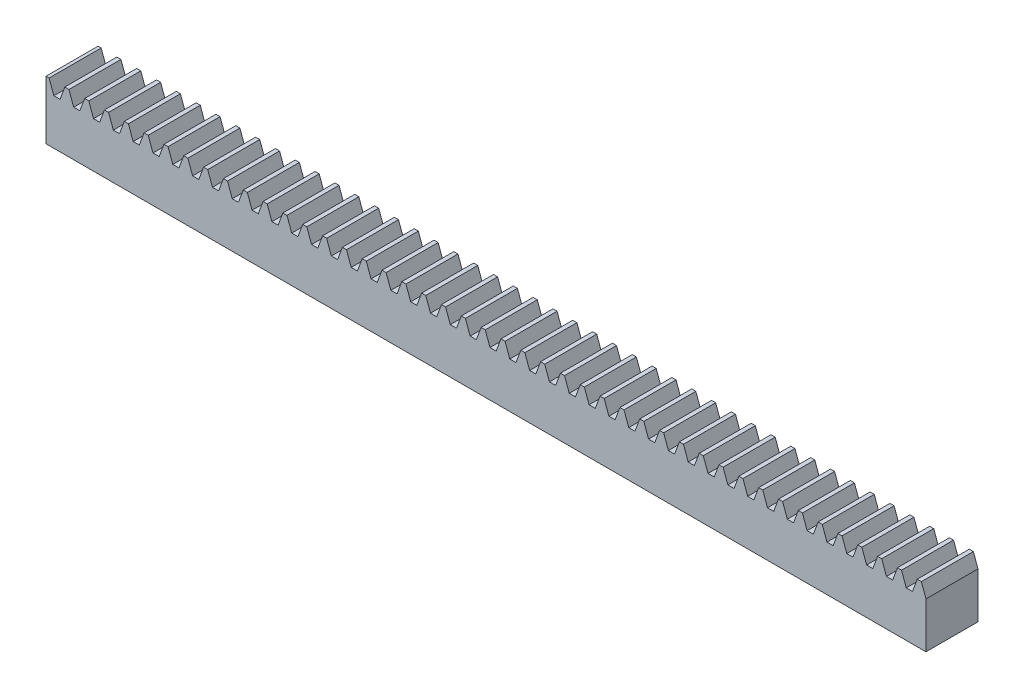
SolidWorks part; units mm, degrees
material "Nylon 101"
ref_plane "Front Plane" through (0, 0, 0) normal (0, 0, 1) x (1, 0, 0)
ref_plane "Top Plane" through (0, 0, 0) normal (0, 1, 0) x (1, 0, 0)
ref_plane "Right Plane" through (0, 0, 0) normal (1, 0, 0) x (0, 0, -1)
sketch "Sketch1" plane through (0, 0, 0) normal (0, 1, 0) x (1, 0, 0)
  line L0 (0, 0) -> (0, 4)
  line L1 (0, 4) -> (67.65, 4)
  line L2 (67.65, 4) -> (67.65, 0)
  line L3 (67.65, 0) -> (0, 0)
  dimension "D1" = 4
  dimension "D2" = 67.65
extrude "Boss-Extrude1" add sketch "Sketch1" along normal blind 4.5
sketch "Sketch2" plane through (0, 0, 0) normal (0, 0, 1) x (1, 0, 0)
  line L0 (0, 4) -> (67.65, 4) construction
  line L1 (0, 4.5) -> (0, 0) construction
  line L2 (67.65, 4.5) -> (67.65, 0) construction
  line L3 (0, 3.5) -> (67.65, 3.5) construction
  line L4 (0, 4.5) -> (67.65, 4.5) construction
  line L5 (0, 4.5) -> (0.239, 4.5) construction
  line L6 (0.239, 4.5) -> (0.603, 3.5)
  line L7 (0.603, 3.5) -> (0.842, 3.5)
  line L8 (1.081, 3.5) -> (1.445, 4.5)
  line L9 (1.445, 4.5) -> (1.684, 4.5) construction
  line L10 (0.842, 3.5) -> (1.081, 3.5)
  line L11 (0.239, 4.5) -> (1.445, 4.5)
  line L12 (1.763, 4.5) -> (2.127, 3.5)
  line L13 (2.127, 3.5) -> (2.366, 3.5)
  line L14 (2.605, 3.5) -> (2.969, 4.5)
  line L15 (2.366, 3.5) -> (2.605, 3.5)
  line L16 (1.763, 4.5) -> (2.969, 4.5)
  line L17 (1.524, 4.5) -> (1.763, 4.5) construction
  line L18 (2.969, 4.5) -> (3.208, 4.5) construction
  line L19 (3.287, 4.5) -> (3.651, 3.5)
  line L20 (3.651, 3.5) -> (3.89, 3.5)
  line L21 (4.129, 3.5) -> (4.493, 4.5)
  line L22 (3.89, 3.5) -> (4.129, 3.5)
  line L23 (3.287, 4.5) -> (4.493, 4.5)
  line L24 (3.048, 4.5) -> (3.287, 4.5) construction
  line L25 (4.493, 4.5) -> (4.732, 4.5) construction
  line L26 (4.811, 4.5) -> (5.175, 3.5)
  line L27 (5.175, 3.5) -> (5.414, 3.5)
  line L28 (5.653, 3.5) -> (6.017, 4.5)
  line L29 (5.414, 3.5) -> (5.653, 3.5)
  line L30 (4.811, 4.5) -> (6.017, 4.5)
  line L31 (4.572, 4.5) -> (4.811, 4.5) construction
  line L32 (6.017, 4.5) -> (6.256, 4.5) construction
  line L33 (6.335, 4.5) -> (6.699, 3.5)
  line L34 (6.699, 3.5) -> (6.938, 3.5)
  line L35 (7.177, 3.5) -> (7.541, 4.5)
  line L36 (6.938, 3.5) -> (7.177, 3.5)
  line L37 (6.335, 4.5) -> (7.541, 4.5)
  line L38 (6.096, 4.5) -> (6.335, 4.5) construction
  line L39 (7.541, 4.5) -> (7.78, 4.5) construction
  line L40 (7.859, 4.5) -> (8.223, 3.5)
  line L41 (8.223, 3.5) -> (8.462, 3.5)
  line L42 (8.701, 3.5) -> (9.065, 4.5)
  line L43 (8.462, 3.5) -> (8.701, 3.5)
  line L44 (7.859, 4.5) -> (9.065, 4.5)
  line L45 (7.62, 4.5) -> (7.859, 4.5) construction
  line L46 (9.065, 4.5) -> (9.304, 4.5) construction
  line L47 (9.383, 4.5) -> (9.747, 3.5)
  line L48 (9.747, 3.5) -> (9.986, 3.5)
  line L49 (10.225, 3.5) -> (10.589, 4.5)
  line L50 (9.986, 3.5) -> (10.225, 3.5)
  line L51 (9.383, 4.5) -> (10.589, 4.5)
  line L52 (9.144, 4.5) -> (9.383, 4.5) construction
  line L53 (10.589, 4.5) -> (10.828, 4.5) construction
  line L54 (10.907, 4.5) -> (11.271, 3.5)
  line L55 (11.271, 3.5) -> (11.51, 3.5)
  line L56 (11.749, 3.5) -> (12.113, 4.5)
  line L57 (11.51, 3.5) -> (11.749, 3.5)
  line L58 (10.907, 4.5) -> (12.113, 4.5)
  line L59 (10.668, 4.5) -> (10.907, 4.5) construction
  line L60 (12.113, 4.5) -> (12.352, 4.5) construction
  line L61 (12.431, 4.5) -> (12.795, 3.5)
  line L62 (12.795, 3.5) -> (13.034, 3.5)
  line L63 (13.273, 3.5) -> (13.637, 4.5)
  line L64 (13.034, 3.5) -> (13.273, 3.5)
  line L65 (12.431, 4.5) -> (13.637, 4.5)
  line L66 (12.192, 4.5) -> (12.431, 4.5) construction
  line L67 (13.637, 4.5) -> (13.876, 4.5) construction
  line L68 (13.955, 4.5) -> (14.319, 3.5)
  line L69 (14.319, 3.5) -> (14.558, 3.5)
  line L70 (14.797, 3.5) -> (15.161, 4.5)
  line L71 (14.558, 3.5) -> (14.797, 3.5)
  line L72 (13.955, 4.5) -> (15.161, 4.5)
  line L73 (13.716, 4.5) -> (13.955, 4.5) construction
  line L74 (15.161, 4.5) -> (15.4, 4.5) construction
  line L75 (15.479, 4.5) -> (15.843, 3.5)
  line L76 (15.843, 3.5) -> (16.082, 3.5)
  line L77 (16.321, 3.5) -> (16.685, 4.5)
  line L78 (16.082, 3.5) -> (16.321, 3.5)
  line L79 (15.479, 4.5) -> (16.685, 4.5)
  line L80 (15.24, 4.5) -> (15.479, 4.5) construction
  line L81 (16.685, 4.5) -> (16.924, 4.5) construction
  line L82 (17.003, 4.5) -> (17.367, 3.5)
  line L83 (17.367, 3.5) -> (17.606, 3.5)
  line L84 (17.845, 3.5) -> (18.209, 4.5)
  line L85 (17.606, 3.5) -> (17.845, 3.5)
  line L86 (17.003, 4.5) -> (18.209, 4.5)
  line L87 (16.764, 4.5) -> (17.003, 4.5) construction
  line L88 (18.209, 4.5) -> (18.448, 4.5) construction
  line L89 (18.527, 4.5) -> (18.891, 3.5)
  line L90 (18.891, 3.5) -> (19.13, 3.5)
  line L91 (19.369, 3.5) -> (19.733, 4.5)
  line L92 (19.13, 3.5) -> (19.369, 3.5)
  line L93 (18.527, 4.5) -> (19.733, 4.5)
  line L94 (18.288, 4.5) -> (18.527, 4.5) construction
  line L95 (19.733, 4.5) -> (19.972, 4.5) construction
  line L96 (20.051, 4.5) -> (20.415, 3.5)
  line L97 (20.415, 3.5) -> (20.654, 3.5)
  line L98 (20.893, 3.5) -> (21.257, 4.5)
  line L99 (20.654, 3.5) -> (20.893, 3.5)
  line L100 (20.051, 4.5) -> (21.257, 4.5)
  line L101 (19.812, 4.5) -> (20.051, 4.5) construction
  line L102 (21.257, 4.5) -> (21.496, 4.5) construction
  line L103 (21.575, 4.5) -> (21.939, 3.5)
  line L104 (21.939, 3.5) -> (22.178, 3.5)
  line L105 (22.417, 3.5) -> (22.781, 4.5)
  line L106 (22.178, 3.5) -> (22.417, 3.5)
  line L107 (21.575, 4.5) -> (22.781, 4.5)
  line L108 (21.336, 4.5) -> (21.575, 4.5) construction
  line L109 (22.781, 4.5) -> (23.02, 4.5) construction
  line L110 (23.099, 4.5) -> (23.463, 3.5)
  line L111 (23.463, 3.5) -> (23.702, 3.5)
  line L112 (23.941, 3.5) -> (24.305, 4.5)
  line L113 (23.702, 3.5) -> (23.941, 3.5)
  line L114 (23.099, 4.5) -> (24.305, 4.5)
  line L115 (22.86, 4.5) -> (23.099, 4.5) construction
  line L116 (24.305, 4.5) -> (24.544, 4.5) construction
  line L117 (24.623, 4.5) -> (24.987, 3.5)
  line L118 (24.987, 3.5) -> (25.226, 3.5)
  line L119 (25.465, 3.5) -> (25.829, 4.5)
  line L120 (25.226, 3.5) -> (25.465, 3.5)
  line L121 (24.623, 4.5) -> (25.829, 4.5)
  line L122 (24.384, 4.5) -> (24.623, 4.5) construction
  line L123 (25.829, 4.5) -> (26.068, 4.5) construction
  line L124 (26.147, 4.5) -> (26.511, 3.5)
  line L125 (26.511, 3.5) -> (26.75, 3.5)
  line L126 (26.989, 3.5) -> (27.353, 4.5)
  line L127 (26.75, 3.5) -> (26.989, 3.5)
  line L128 (26.147, 4.5) -> (27.353, 4.5)
  line L129 (25.908, 4.5) -> (26.147, 4.5) construction
  line L130 (27.353, 4.5) -> (27.592, 4.5) construction
  line L131 (27.671, 4.5) -> (28.035, 3.5)
  line L132 (28.035, 3.5) -> (28.274, 3.5)
  line L133 (28.513, 3.5) -> (28.877, 4.5)
  line L134 (28.274, 3.5) -> (28.513, 3.5)
  line L135 (27.671, 4.5) -> (28.877, 4.5)
  line L136 (27.432, 4.5) -> (27.671, 4.5) construction
  line L137 (28.877, 4.5) -> (29.116, 4.5) construction
  line L138 (29.195, 4.5) -> (29.559, 3.5)
  line L139 (29.559, 3.5) -> (29.798, 3.5)
  line L140 (30.037, 3.5) -> (30.401, 4.5)
  line L141 (29.798, 3.5) -> (30.037, 3.5)
  line L142 (29.195, 4.5) -> (30.401, 4.5)
  line L143 (28.956, 4.5) -> (29.195, 4.5) construction
  line L144 (30.401, 4.5) -> (30.64, 4.5) construction
  line L145 (30.719, 4.5) -> (31.083, 3.5)
  line L146 (31.083, 3.5) -> (31.322, 3.5)
  line L147 (31.561, 3.5) -> (31.925, 4.5)
  line L148 (31.322, 3.5) -> (31.561, 3.5)
  line L149 (30.719, 4.5) -> (31.925, 4.5)
  line L150 (30.48, 4.5) -> (30.719, 4.5) construction
  line L151 (31.925, 4.5) -> (32.164, 4.5) construction
  line L152 (32.243, 4.5) -> (32.607, 3.5)
  line L153 (32.607, 3.5) -> (32.846, 3.5)
  line L154 (33.085, 3.5) -> (33.449, 4.5)
  line L155 (32.846, 3.5) -> (33.085, 3.5)
  line L156 (32.243, 4.5) -> (33.449, 4.5)
  line L157 (32.004, 4.5) -> (32.243, 4.5) construction
  line L158 (33.449, 4.5) -> (33.688, 4.5) construction
  line L159 (33.767, 4.5) -> (34.131, 3.5)
  line L160 (34.131, 3.5) -> (34.37, 3.5)
  line L161 (34.609, 3.5) -> (34.973, 4.5)
  line L162 (34.37, 3.5) -> (34.609, 3.5)
  line L163 (33.767, 4.5) -> (34.973, 4.5)
  line L164 (33.528, 4.5) -> (33.767, 4.5) construction
  line L165 (34.973, 4.5) -> (35.212, 4.5) construction
  line L166 (35.291, 4.5) -> (35.655, 3.5)
  line L167 (35.655, 3.5) -> (35.894, 3.5)
  line L168 (36.133, 3.5) -> (36.497, 4.5)
  line L169 (35.894, 3.5) -> (36.133, 3.5)
  line L170 (35.291, 4.5) -> (36.497, 4.5)
  line L171 (35.052, 4.5) -> (35.291, 4.5) construction
  line L172 (36.497, 4.5) -> (36.736, 4.5) construction
  line L173 (36.815, 4.5) -> (37.179, 3.5)
  line L174 (37.179, 3.5) -> (37.418, 3.5)
  line L175 (37.657, 3.5) -> (38.021, 4.5)
  line L176 (37.418, 3.5) -> (37.657, 3.5)
  line L177 (36.815, 4.5) -> (38.021, 4.5)
  line L178 (36.576, 4.5) -> (36.815, 4.5) construction
  line L179 (38.021, 4.5) -> (38.26, 4.5) construction
  line L180 (38.339, 4.5) -> (38.703, 3.5)
  line L181 (38.703, 3.5) -> (38.942, 3.5)
  line L182 (39.181, 3.5) -> (39.545, 4.5)
  line L183 (38.942, 3.5) -> (39.181, 3.5)
  line L184 (38.339, 4.5) -> (39.545, 4.5)
  line L185 (38.1, 4.5) -> (38.339, 4.5) construction
  line L186 (39.545, 4.5) -> (39.784, 4.5) construction
  line L187 (39.863, 4.5) -> (40.227, 3.5)
  line L188 (40.227, 3.5) -> (40.466, 3.5)
  line L189 (40.705, 3.5) -> (41.069, 4.5)
  line L190 (40.466, 3.5) -> (40.705, 3.5)
  line L191 (39.863, 4.5) -> (41.069, 4.5)
  line L192 (39.624, 4.5) -> (39.863, 4.5) construction
  line L193 (41.069, 4.5) -> (41.308, 4.5) construction
  line L194 (41.387, 4.5) -> (41.751, 3.5)
  line L195 (41.751, 3.5) -> (41.99, 3.5)
  line L196 (42.229, 3.5) -> (42.593, 4.5)
  line L197 (41.99, 3.5) -> (42.229, 3.5)
  line L198 (41.387, 4.5) -> (42.593, 4.5)
  line L199 (41.148, 4.5) -> (41.387, 4.5) construction
  line L200 (42.593, 4.5) -> (42.832, 4.5) construction
  line L201 (42.911, 4.5) -> (43.275, 3.5)
  line L202 (43.275, 3.5) -> (43.514, 3.5)
  line L203 (43.753, 3.5) -> (44.117, 4.5)
  line L204 (43.514, 3.5) -> (43.753, 3.5)
  line L205 (42.911, 4.5) -> (44.117, 4.5)
  line L206 (42.672, 4.5) -> (42.911, 4.5) construction
  line L207 (44.117, 4.5) -> (44.356, 4.5) construction
  line L208 (44.435, 4.5) -> (44.799, 3.5)
  line L209 (44.799, 3.5) -> (45.038, 3.5)
  line L210 (45.277, 3.5) -> (45.641, 4.5)
  line L211 (45.038, 3.5) -> (45.277, 3.5)
  line L212 (44.435, 4.5) -> (45.641, 4.5)
  line L213 (44.196, 4.5) -> (44.435, 4.5) construction
  line L214 (45.641, 4.5) -> (45.88, 4.5) construction
  line L215 (45.959, 4.5) -> (46.323, 3.5)
  line L216 (46.323, 3.5) -> (46.562, 3.5)
  line L217 (46.801, 3.5) -> (47.165, 4.5)
  line L218 (46.562, 3.5) -> (46.801, 3.5)
  line L219 (45.959, 4.5) -> (47.165, 4.5)
  line L220 (45.72, 4.5) -> (45.959, 4.5) construction
  line L221 (47.165, 4.5) -> (47.404, 4.5) construction
  line L222 (47.483, 4.5) -> (47.847, 3.5)
  line L223 (47.847, 3.5) -> (48.086, 3.5)
  line L224 (48.325, 3.5) -> (48.689, 4.5)
  line L225 (48.086, 3.5) -> (48.325, 3.5)
  line L226 (47.483, 4.5) -> (48.689, 4.5)
  line L227 (47.244, 4.5) -> (47.483, 4.5) construction
  line L228 (48.689, 4.5) -> (48.928, 4.5) construction
  line L229 (49.007, 4.5) -> (49.371, 3.5)
  line L230 (49.371, 3.5) -> (49.61, 3.5)
  line L231 (49.849, 3.5) -> (50.213, 4.5)
  line L232 (49.61, 3.5) -> (49.849, 3.5)
  line L233 (49.007, 4.5) -> (50.213, 4.5)
  line L234 (48.768, 4.5) -> (49.007, 4.5) construction
  line L235 (50.213, 4.5) -> (50.452, 4.5) construction
  line L236 (50.531, 4.5) -> (50.895, 3.5)
  line L237 (50.895, 3.5) -> (51.134, 3.5)
  line L238 (51.373, 3.5) -> (51.737, 4.5)
  line L239 (51.134, 3.5) -> (51.373, 3.5)
  line L240 (50.531, 4.5) -> (51.737, 4.5)
  line L241 (50.292, 4.5) -> (50.531, 4.5) construction
  line L242 (51.737, 4.5) -> (51.976, 4.5) construction
  line L243 (52.055, 4.5) -> (52.419, 3.5)
  line L244 (52.419, 3.5) -> (52.658, 3.5)
  line L245 (52.897, 3.5) -> (53.261, 4.5)
  line L246 (52.658, 3.5) -> (52.897, 3.5)
  line L247 (52.055, 4.5) -> (53.261, 4.5)
  line L248 (51.816, 4.5) -> (52.055, 4.5) construction
  line L249 (53.261, 4.5) -> (53.5, 4.5) construction
  line L250 (53.579, 4.5) -> (53.943, 3.5)
  line L251 (53.943, 3.5) -> (54.182, 3.5)
  line L252 (54.421, 3.5) -> (54.785, 4.5)
  line L253 (54.182, 3.5) -> (54.421, 3.5)
  line L254 (53.579, 4.5) -> (54.785, 4.5)
  line L255 (53.34, 4.5) -> (53.579, 4.5) construction
  line L256 (54.785, 4.5) -> (55.024, 4.5) construction
  line L257 (55.103, 4.5) -> (55.467, 3.5)
  line L258 (55.467, 3.5) -> (55.706, 3.5)
  line L259 (55.945, 3.5) -> (56.309, 4.5)
  line L260 (55.706, 3.5) -> (55.945, 3.5)
  line L261 (55.103, 4.5) -> (56.309, 4.5)
  line L262 (54.864, 4.5) -> (55.103, 4.5) construction
  line L263 (56.309, 4.5) -> (56.548, 4.5) construction
  line L264 (56.627, 4.5) -> (56.991, 3.5)
  line L265 (56.991, 3.5) -> (57.23, 3.5)
  line L266 (57.469, 3.5) -> (57.833, 4.5)
  line L267 (57.23, 3.5) -> (57.469, 3.5)
  line L268 (56.627, 4.5) -> (57.833, 4.5)
  line L269 (56.388, 4.5) -> (56.627, 4.5) construction
  line L270 (57.833, 4.5) -> (58.072, 4.5) construction
  line L271 (58.151, 4.5) -> (58.515, 3.5)
  line L272 (58.515, 3.5) -> (58.754, 3.5)
  line L273 (58.993, 3.5) -> (59.357, 4.5)
  line L274 (58.754, 3.5) -> (58.993, 3.5)
  line L275 (58.151, 4.5) -> (59.357, 4.5)
  line L276 (57.912, 4.5) -> (58.151, 4.5) construction
  line L277 (59.357, 4.5) -> (59.596, 4.5) construction
  line L278 (59.675, 4.5) -> (60.039, 3.5)
  line L279 (60.039, 3.5) -> (60.278, 3.5)
  line L280 (60.517, 3.5) -> (60.881, 4.5)
  line L281 (60.278, 3.5) -> (60.517, 3.5)
  line L282 (59.675, 4.5) -> (60.881, 4.5)
  line L283 (59.436, 4.5) -> (59.675, 4.5) construction
  line L284 (60.881, 4.5) -> (61.12, 4.5) construction
  line L285 (61.199, 4.5) -> (61.563, 3.5)
  line L286 (61.563, 3.5) -> (61.802, 3.5)
  line L287 (62.041, 3.5) -> (62.405, 4.5)
  line L288 (61.802, 3.5) -> (62.041, 3.5)
  line L289 (61.199, 4.5) -> (62.405, 4.5)
  line L290 (60.96, 4.5) -> (61.199, 4.5) construction
  line L291 (62.405, 4.5) -> (62.644, 4.5) construction
  line L292 (62.723, 4.5) -> (63.087, 3.5)
  line L293 (63.087, 3.5) -> (63.326, 3.5)
  line L294 (63.565, 3.5) -> (63.929, 4.5)
  line L295 (63.326, 3.5) -> (63.565, 3.5)
  line L296 (62.723, 4.5) -> (63.929, 4.5)
  line L297 (62.484, 4.5) -> (62.723, 4.5) construction
  line L298 (63.929, 4.5) -> (64.168, 4.5) construction
  line L299 (64.247, 4.5) -> (64.611, 3.5)
  line L300 (64.611, 3.5) -> (64.85, 3.5)
  line L301 (65.089, 3.5) -> (65.453, 4.5)
  line L302 (64.85, 3.5) -> (65.089, 3.5)
  line L303 (64.247, 4.5) -> (65.453, 4.5)
  line L304 (64.008, 4.5) -> (64.247, 4.5) construction
  line L305 (65.453, 4.5) -> (65.692, 4.5) construction
  line L306 (65.771, 4.5) -> (66.135, 3.5)
  line L307 (66.135, 3.5) -> (66.374, 3.5)
  line L308 (66.613, 3.5) -> (66.977, 4.5)
  line L309 (66.374, 3.5) -> (66.613, 3.5)
  line L310 (65.771, 4.5) -> (66.977, 4.5)
  line L311 (65.532, 4.5) -> (65.771, 4.5) construction
  line L312 (66.977, 4.5) -> (67.216, 4.5) construction
  line L313 (67.295, 4.5) -> (67.659, 3.5)
  line L314 (67.659, 3.5) -> (67.898, 3.5)
  line L315 (68.137, 3.5) -> (68.501, 4.5)
  line L316 (67.898, 3.5) -> (68.137, 3.5)
  line L317 (67.295, 4.5) -> (68.501, 4.5)
  line L318 (67.056, 4.5) -> (67.295, 4.5) construction
  line L319 (68.501, 4.5) -> (68.74, 4.5) construction
  line L320 (68.819, 4.5) -> (69.183, 3.5)
  line L321 (69.183, 3.5) -> (69.422, 3.5)
  line L322 (69.661, 3.5) -> (70.025, 4.5)
  line L323 (69.422, 3.5) -> (69.661, 3.5)
  line L324 (68.819, 4.5) -> (70.025, 4.5)
  line L325 (68.58, 4.5) -> (68.819, 4.5) construction
  line L326 (70.025, 4.5) -> (70.264, 4.5) construction
  line L327 (70.343, 4.5) -> (70.707, 3.5)
  line L328 (70.707, 3.5) -> (70.946, 3.5)
  line L329 (71.185, 3.5) -> (71.549, 4.5)
  line L330 (70.946, 3.5) -> (71.185, 3.5)
  line L331 (70.343, 4.5) -> (71.549, 4.5)
  line L332 (70.104, 4.5) -> (70.343, 4.5) construction
  line L333 (71.549, 4.5) -> (71.788, 4.5) construction
  line L334 (71.867, 4.5) -> (72.231, 3.5)
  line L335 (72.231, 3.5) -> (72.47, 3.5)
  line L336 (72.709, 3.5) -> (73.073, 4.5)
  line L337 (72.47, 3.5) -> (72.709, 3.5)
  line L338 (71.867, 4.5) -> (73.073, 4.5)
  line L339 (71.628, 4.5) -> (71.867, 4.5) construction
  line L340 (73.073, 4.5) -> (73.312, 4.5) construction
  line L341 (73.391, 4.5) -> (73.755, 3.5)
  line L342 (73.755, 3.5) -> (73.994, 3.5)
  line L343 (74.233, 3.5) -> (74.597, 4.5)
  line L344 (73.994, 3.5) -> (74.233, 3.5)
  line L345 (73.391, 4.5) -> (74.597, 4.5)
  line L346 (73.152, 4.5) -> (73.391, 4.5) construction
  line L347 (74.597, 4.5) -> (74.836, 4.5) construction
  line L348 (74.915, 4.5) -> (75.279, 3.5)
  line L349 (75.279, 3.5) -> (75.518, 3.5)
  line L350 (75.757, 3.5) -> (76.121, 4.5)
  line L351 (75.518, 3.5) -> (75.757, 3.5)
  line L352 (74.915, 4.5) -> (76.121, 4.5)
  line L353 (74.676, 4.5) -> (74.915, 4.5) construction
  line L354 (76.121, 4.5) -> (76.36, 4.5) construction
  line L355 (76.439, 4.5) -> (76.803, 3.5)
  line L356 (76.803, 3.5) -> (77.042, 3.5)
  line L357 (77.281, 3.5) -> (77.645, 4.5)
  line L358 (77.042, 3.5) -> (77.281, 3.5)
  line L359 (76.439, 4.5) -> (77.645, 4.5)
  line L360 (76.2, 4.5) -> (76.439, 4.5) construction
  line L361 (77.645, 4.5) -> (77.884, 4.5) construction
  line L362 (77.963, 4.5) -> (78.327, 3.5)
  line L363 (78.327, 3.5) -> (78.566, 3.5)
  line L364 (78.805, 3.5) -> (79.169, 4.5)
  line L365 (78.566, 3.5) -> (78.805, 3.5)
  line L366 (77.963, 4.5) -> (79.169, 4.5)
  line L367 (77.724, 4.5) -> (77.963, 4.5) construction
  line L368 (79.169, 4.5) -> (79.408, 4.5) construction
  line L369 (79.487, 4.5) -> (79.851, 3.5)
  line L370 (79.851, 3.5) -> (80.09, 3.5)
  line L371 (80.329, 3.5) -> (80.693, 4.5)
  line L372 (80.09, 3.5) -> (80.329, 3.5)
  line L373 (79.487, 4.5) -> (80.693, 4.5)
  line L374 (79.248, 4.5) -> (79.487, 4.5) construction
  line L375 (80.693, 4.5) -> (80.932, 4.5) construction
  line L376 (81.011, 4.5) -> (81.375, 3.5)
  line L377 (81.375, 3.5) -> (81.614, 3.5)
  line L378 (81.853, 3.5) -> (82.217, 4.5)
  line L379 (81.614, 3.5) -> (81.853, 3.5)
  line L380 (81.011, 4.5) -> (82.217, 4.5)
  line L381 (80.772, 4.5) -> (81.011, 4.5) construction
  line L382 (82.217, 4.5) -> (82.456, 4.5) construction
  line L383 (82.535, 4.5) -> (82.899, 3.5)
  line L384 (82.899, 3.5) -> (83.138, 3.5)
  line L385 (83.377, 3.5) -> (83.741, 4.5)
  line L386 (83.138, 3.5) -> (83.377, 3.5)
  line L387 (82.535, 4.5) -> (83.741, 4.5)
  line L388 (82.296, 4.5) -> (82.535, 4.5) construction
  line L389 (83.741, 4.5) -> (83.98, 4.5) construction
  line L390 (84.059, 4.5) -> (84.423, 3.5)
  line L391 (84.423, 3.5) -> (84.662, 3.5)
  line L392 (84.901, 3.5) -> (85.265, 4.5)
  line L393 (84.662, 3.5) -> (84.901, 3.5)
  line L394 (84.059, 4.5) -> (85.265, 4.5)
  line L395 (83.82, 4.5) -> (84.059, 4.5) construction
  line L396 (85.265, 4.5) -> (85.504, 4.5) construction
  line L397 (85.583, 4.5) -> (85.947, 3.5)
  line L398 (85.947, 3.5) -> (86.186, 3.5)
  line L399 (86.425, 3.5) -> (86.789, 4.5)
  line L400 (86.186, 3.5) -> (86.425, 3.5)
  line L401 (85.583, 4.5) -> (86.789, 4.5)
  line L402 (85.344, 4.5) -> (85.583, 4.5) construction
  line L403 (86.789, 4.5) -> (87.028, 4.5) construction
  line L404 (87.107, 4.5) -> (87.471, 3.5)
  line L405 (87.471, 3.5) -> (87.71, 3.5)
  line L406 (87.949, 3.5) -> (88.313, 4.5)
  line L407 (87.71, 3.5) -> (87.949, 3.5)
  line L408 (87.107, 4.5) -> (88.313, 4.5)
  line L409 (86.868, 4.5) -> (87.107, 4.5) construction
  line L410 (88.313, 4.5) -> (88.552, 4.5) construction
  line L411 (88.631, 4.5) -> (88.995, 3.5)
  line L412 (88.995, 3.5) -> (89.234, 3.5)
  line L413 (89.473, 3.5) -> (89.837, 4.5)
  line L414 (89.234, 3.5) -> (89.473, 3.5)
  line L415 (88.631, 4.5) -> (89.837, 4.5)
  line L416 (88.392, 4.5) -> (88.631, 4.5) construction
  line L417 (89.837, 4.5) -> (90.076, 4.5) construction
  line L418 (90.155, 4.5) -> (90.519, 3.5)
  line L419 (90.519, 3.5) -> (90.758, 3.5)
  line L420 (90.997, 3.5) -> (91.361, 4.5)
  line L421 (90.758, 3.5) -> (90.997, 3.5)
  line L422 (90.155, 4.5) -> (91.361, 4.5)
  line L423 (89.916, 4.5) -> (90.155, 4.5) construction
  line L424 (91.361, 4.5) -> (91.6, 4.5) construction
  line L425 (91.679, 4.5) -> (92.043, 3.5)
  line L426 (92.043, 3.5) -> (92.282, 3.5)
  line L427 (92.521, 3.5) -> (92.885, 4.5)
  line L428 (92.282, 3.5) -> (92.521, 3.5)
  line L429 (91.679, 4.5) -> (92.885, 4.5)
  line L430 (91.44, 4.5) -> (91.679, 4.5) construction
  line L431 (92.885, 4.5) -> (93.124, 4.5) construction
  line L432 (93.203, 4.5) -> (93.567, 3.5)
  line L433 (93.567, 3.5) -> (93.806, 3.5)
  line L434 (94.045, 3.5) -> (94.409, 4.5)
  line L435 (93.806, 3.5) -> (94.045, 3.5)
  line L436 (93.203, 4.5) -> (94.409, 4.5)
  line L437 (92.964, 4.5) -> (93.203, 4.5) construction
  line L438 (94.409, 4.5) -> (94.648, 4.5) construction
  line L439 (94.727, 4.5) -> (95.091, 3.5)
  line L440 (95.091, 3.5) -> (95.33, 3.5)
  line L441 (95.569, 3.5) -> (95.933, 4.5)
  line L442 (95.33, 3.5) -> (95.569, 3.5)
  line L443 (94.727, 4.5) -> (95.933, 4.5)
  line L444 (94.488, 4.5) -> (94.727, 4.5) construction
  line L445 (95.933, 4.5) -> (96.172, 4.5) construction
  line L446 (96.251, 4.5) -> (96.615, 3.5)
  line L447 (96.615, 3.5) -> (96.854, 3.5)
  line L448 (97.093, 3.5) -> (97.457, 4.5)
  line L449 (96.854, 3.5) -> (97.093, 3.5)
  line L450 (96.251, 4.5) -> (97.457, 4.5)
  line L451 (96.012, 4.5) -> (96.251, 4.5) construction
  line L452 (97.457, 4.5) -> (97.696, 4.5) construction
  line L453 (97.775, 4.5) -> (98.139, 3.5)
  line L454 (98.139, 3.5) -> (98.378, 3.5)
  line L455 (98.617, 3.5) -> (98.981, 4.5)
  line L456 (98.378, 3.5) -> (98.617, 3.5)
  line L457 (97.775, 4.5) -> (98.981, 4.5)
  line L458 (97.536, 4.5) -> (97.775, 4.5) construction
  line L459 (98.981, 4.5) -> (99.22, 4.5) construction
  line L460 (99.299, 4.5) -> (99.663, 3.5)
  line L461 (99.663, 3.5) -> (99.902, 3.5)
  line L462 (100.141, 3.5) -> (100.505, 4.5)
  line L463 (99.902, 3.5) -> (100.141, 3.5)
  line L464 (99.299, 4.5) -> (100.505, 4.5)
  line L465 (99.06, 4.5) -> (99.299, 4.5) construction
  line L466 (100.505, 4.5) -> (100.744, 4.5) construction
  line L467 (100.823, 4.5) -> (101.187, 3.5)
  line L468 (101.187, 3.5) -> (101.426, 3.5)
  line L469 (101.665, 3.5) -> (102.029, 4.5)
  line L470 (101.426, 3.5) -> (101.665, 3.5)
  line L471 (100.823, 4.5) -> (102.029, 4.5)
  line L472 (100.584, 4.5) -> (100.823, 4.5) construction
  line L473 (102.029, 4.5) -> (102.268, 4.5) construction
  line L474 (102.347, 4.5) -> (102.711, 3.5)
  line L475 (102.711, 3.5) -> (102.95, 3.5)
  line L476 (103.189, 3.5) -> (103.553, 4.5)
  line L477 (102.95, 3.5) -> (103.189, 3.5)
  line L478 (102.347, 4.5) -> (103.553, 4.5)
  line L479 (102.108, 4.5) -> (102.347, 4.5) construction
  line L480 (103.553, 4.5) -> (103.792, 4.5) construction
  line L481 (103.871, 4.5) -> (104.235, 3.5)
  line L482 (104.235, 3.5) -> (104.474, 3.5)
  line L483 (104.713, 3.5) -> (105.077, 4.5)
  line L484 (104.474, 3.5) -> (104.713, 3.5)
  line L485 (103.871, 4.5) -> (105.077, 4.5)
  line L486 (103.632, 4.5) -> (103.871, 4.5) construction
  line L487 (105.077, 4.5) -> (105.316, 4.5) construction
  line L488 (105.395, 4.5) -> (105.759, 3.5)
  line L489 (105.759, 3.5) -> (105.998, 3.5)
  line L490 (106.237, 3.5) -> (106.601, 4.5)
  line L491 (105.998, 3.5) -> (106.237, 3.5)
  line L492 (105.395, 4.5) -> (106.601, 4.5)
  line L493 (105.156, 4.5) -> (105.395, 4.5) construction
  line L494 (106.601, 4.5) -> (106.84, 4.5) construction
  line L495 (106.919, 4.5) -> (107.283, 3.5)
  line L496 (107.283, 3.5) -> (107.522, 3.5)
  line L497 (107.761, 3.5) -> (108.125, 4.5)
  line L498 (107.522, 3.5) -> (107.761, 3.5)
  line L499 (106.919, 4.5) -> (108.125, 4.5)
  line L500 (106.68, 4.5) -> (106.919, 4.5) construction
  line L501 (108.125, 4.5) -> (108.364, 4.5) construction
  line L502 (108.443, 4.5) -> (108.807, 3.5)
  line L503 (108.807, 3.5) -> (109.046, 3.5)
  line L504 (109.285, 3.5) -> (109.649, 4.5)
  line L505 (109.046, 3.5) -> (109.285, 3.5)
  line L506 (108.443, 4.5) -> (109.649, 4.5)
  line L507 (108.204, 4.5) -> (108.443, 4.5) construction
  line L508 (109.649, 4.5) -> (109.888, 4.5) construction
  line L509 (109.967, 4.5) -> (110.331, 3.5)
  line L510 (110.331, 3.5) -> (110.57, 3.5)
  line L511 (110.809, 3.5) -> (111.173, 4.5)
  line L512 (110.57, 3.5) -> (110.809, 3.5)
  line L513 (109.967, 4.5) -> (111.173, 4.5)
  line L514 (109.728, 4.5) -> (109.967, 4.5) construction
  line L515 (111.173, 4.5) -> (111.412, 4.5) construction
  line L516 (111.491, 4.5) -> (111.855, 3.5)
  line L517 (111.855, 3.5) -> (112.094, 3.5)
  line L518 (112.333, 3.5) -> (112.697, 4.5)
  line L519 (112.094, 3.5) -> (112.333, 3.5)
  line L520 (111.491, 4.5) -> (112.697, 4.5)
  line L521 (111.252, 4.5) -> (111.491, 4.5) construction
  line L522 (112.697, 4.5) -> (112.936, 4.5) construction
  line L523 (113.015, 4.5) -> (113.379, 3.5)
  line L524 (113.379, 3.5) -> (113.618, 3.5)
  line L525 (113.857, 3.5) -> (114.221, 4.5)
  line L526 (113.618, 3.5) -> (113.857, 3.5)
  line L527 (113.015, 4.5) -> (114.221, 4.5)
  line L528 (112.776, 4.5) -> (113.015, 4.5) construction
  line L529 (114.221, 4.5) -> (114.46, 4.5) construction
  line L530 (114.539, 4.5) -> (114.903, 3.5)
  line L531 (114.903, 3.5) -> (115.142, 3.5)
  line L532 (115.381, 3.5) -> (115.745, 4.5)
  line L533 (115.142, 3.5) -> (115.381, 3.5)
  line L534 (114.539, 4.5) -> (115.745, 4.5)
  line L535 (114.3, 4.5) -> (114.539, 4.5) construction
  line L536 (115.745, 4.5) -> (115.984, 4.5) construction
  line L537 (116.063, 4.5) -> (116.427, 3.5)
  line L538 (116.427, 3.5) -> (116.666, 3.5)
  line L539 (116.905, 3.5) -> (117.269, 4.5)
  line L540 (116.666, 3.5) -> (116.905, 3.5)
  line L541 (116.063, 4.5) -> (117.269, 4.5)
  line L542 (115.824, 4.5) -> (116.063, 4.5) construction
  line L543 (117.269, 4.5) -> (117.508, 4.5) construction
  line L544 (117.587, 4.5) -> (117.951, 3.5)
  line L545 (117.951, 3.5) -> (118.19, 3.5)
  line L546 (118.429, 3.5) -> (118.793, 4.5)
  line L547 (118.19, 3.5) -> (118.429, 3.5)
  line L548 (117.587, 4.5) -> (118.793, 4.5)
  line L549 (117.348, 4.5) -> (117.587, 4.5) construction
  line L550 (118.793, 4.5) -> (119.032, 4.5) construction
  line L551 (119.111, 4.5) -> (119.475, 3.5)
  line L552 (119.475, 3.5) -> (119.714, 3.5)
  line L553 (119.953, 3.5) -> (120.317, 4.5)
  line L554 (119.714, 3.5) -> (119.953, 3.5)
  line L555 (119.111, 4.5) -> (120.317, 4.5)
  line L556 (118.872, 4.5) -> (119.111, 4.5) construction
  line L557 (120.317, 4.5) -> (120.556, 4.5) construction
  line L558 (120.635, 4.5) -> (120.999, 3.5)
  line L559 (120.999, 3.5) -> (121.238, 3.5)
  line L560 (121.477, 3.5) -> (121.841, 4.5)
  line L561 (121.238, 3.5) -> (121.477, 3.5)
  line L562 (120.635, 4.5) -> (121.841, 4.5)
  line L563 (120.396, 4.5) -> (120.635, 4.5) construction
  line L564 (121.841, 4.5) -> (122.08, 4.5) construction
  line L565 (122.159, 4.5) -> (122.523, 3.5)
  line L566 (122.523, 3.5) -> (122.762, 3.5)
  line L567 (123.001, 3.5) -> (123.365, 4.5)
  line L568 (122.762, 3.5) -> (123.001, 3.5)
  line L569 (122.159, 4.5) -> (123.365, 4.5)
  line L570 (121.92, 4.5) -> (122.159, 4.5) construction
  line L571 (123.365, 4.5) -> (123.604, 4.5) construction
  line L572 (123.683, 4.5) -> (124.047, 3.5)
  line L573 (124.047, 3.5) -> (124.286, 3.5)
  line L574 (124.525, 3.5) -> (124.889, 4.5)
  line L575 (124.286, 3.5) -> (124.525, 3.5)
  line L576 (123.683, 4.5) -> (124.889, 4.5)
  line L577 (123.444, 4.5) -> (123.683, 4.5) construction
  line L578 (124.889, 4.5) -> (125.128, 4.5) construction
  line L579 (125.207, 4.5) -> (125.571, 3.5)
  line L580 (125.571, 3.5) -> (125.81, 3.5)
  line L581 (126.049, 3.5) -> (126.413, 4.5)
  line L582 (125.81, 3.5) -> (126.049, 3.5)
  line L583 (125.207, 4.5) -> (126.413, 4.5)
  line L584 (124.968, 4.5) -> (125.207, 4.5) construction
  line L585 (126.413, 4.5) -> (126.652, 4.5) construction
  line L586 (126.731, 4.5) -> (127.095, 3.5)
  line L587 (127.095, 3.5) -> (127.334, 3.5)
  line L588 (127.573, 3.5) -> (127.937, 4.5)
  line L589 (127.334, 3.5) -> (127.573, 3.5)
  line L590 (126.731, 4.5) -> (127.937, 4.5)
  line L591 (126.492, 4.5) -> (126.731, 4.5) construction
  line L592 (127.937, 4.5) -> (128.176, 4.5) construction
  line L593 (128.255, 4.5) -> (128.619, 3.5)
  line L594 (128.619, 3.5) -> (128.858, 3.5)
  line L595 (129.097, 3.5) -> (129.461, 4.5)
  line L596 (128.858, 3.5) -> (129.097, 3.5)
  line L597 (128.255, 4.5) -> (129.461, 4.5)
  line L598 (128.016, 4.5) -> (128.255, 4.5) construction
  line L599 (129.461, 4.5) -> (129.7, 4.5) construction
  line L600 (129.779, 4.5) -> (130.143, 3.5)
  line L601 (130.143, 3.5) -> (130.382, 3.5)
  line L602 (130.621, 3.5) -> (130.985, 4.5)
  line L603 (130.382, 3.5) -> (130.621, 3.5)
  line L604 (129.779, 4.5) -> (130.985, 4.5)
  line L605 (129.54, 4.5) -> (129.779, 4.5) construction
  line L606 (130.985, 4.5) -> (131.224, 4.5) construction
  line L607 (131.303, 4.5) -> (131.667, 3.5)
  line L608 (131.667, 3.5) -> (131.906, 3.5)
  line L609 (132.145, 3.5) -> (132.509, 4.5)
  line L610 (131.906, 3.5) -> (132.145, 3.5)
  line L611 (131.303, 4.5) -> (132.509, 4.5)
  line L612 (131.064, 4.5) -> (131.303, 4.5) construction
  line L613 (132.509, 4.5) -> (132.748, 4.5) construction
  line L614 (132.827, 4.5) -> (133.191, 3.5)
  line L615 (133.191, 3.5) -> (133.43, 3.5)
  line L616 (133.669, 3.5) -> (134.033, 4.5)
  line L617 (133.43, 3.5) -> (133.669, 3.5)
  line L618 (132.827, 4.5) -> (134.033, 4.5)
  line L619 (132.588, 4.5) -> (132.827, 4.5) construction
  line L620 (134.033, 4.5) -> (134.272, 4.5) construction
  line L621 (134.351, 4.5) -> (134.715, 3.5)
  line L622 (134.715, 3.5) -> (134.954, 3.5)
  line L623 (135.193, 3.5) -> (135.557, 4.5)
  line L624 (134.954, 3.5) -> (135.193, 3.5)
  line L625 (134.351, 4.5) -> (135.557, 4.5)
  line L626 (134.112, 4.5) -> (134.351, 4.5) construction
  line L627 (135.557, 4.5) -> (135.796, 4.5) construction
  line L628 (135.875, 4.5) -> (136.239, 3.5)
  line L629 (136.239, 3.5) -> (136.478, 3.5)
  line L630 (136.717, 3.5) -> (137.081, 4.5)
  line L631 (136.478, 3.5) -> (136.717, 3.5)
  line L632 (135.875, 4.5) -> (137.081, 4.5)
  line L633 (135.636, 4.5) -> (135.875, 4.5) construction
  line L634 (137.081, 4.5) -> (137.32, 4.5) construction
  line L635 (137.399, 4.5) -> (137.763, 3.5)
  line L636 (137.763, 3.5) -> (138.002, 3.5)
  line L637 (138.241, 3.5) -> (138.605, 4.5)
  line L638 (138.002, 3.5) -> (138.241, 3.5)
  line L639 (137.399, 4.5) -> (138.605, 4.5)
  line L640 (137.16, 4.5) -> (137.399, 4.5) construction
  line L641 (138.605, 4.5) -> (138.844, 4.5) construction
  line L642 (138.923, 4.5) -> (139.287, 3.5)
  line L643 (139.287, 3.5) -> (139.526, 3.5)
  line L644 (139.765, 3.5) -> (140.129, 4.5)
  line L645 (139.526, 3.5) -> (139.765, 3.5)
  line L646 (138.923, 4.5) -> (140.129, 4.5)
  line L647 (138.684, 4.5) -> (138.923, 4.5) construction
  line L648 (140.129, 4.5) -> (140.368, 4.5) construction
  line L649 (140.447, 4.5) -> (140.811, 3.5)
  line L650 (140.811, 3.5) -> (141.05, 3.5)
  line L651 (141.289, 3.5) -> (141.653, 4.5)
  line L652 (141.05, 3.5) -> (141.289, 3.5)
  line L653 (140.447, 4.5) -> (141.653, 4.5)
  line L654 (140.208, 4.5) -> (140.447, 4.5) construction
  line L655 (141.653, 4.5) -> (141.892, 4.5) construction
  line L656 (141.971, 4.5) -> (142.335, 3.5)
  line L657 (142.335, 3.5) -> (142.574, 3.5)
  line L658 (142.813, 3.5) -> (143.177, 4.5)
  line L659 (142.574, 3.5) -> (142.813, 3.5)
  line L660 (141.971, 4.5) -> (143.177, 4.5)
  line L661 (141.732, 4.5) -> (141.971, 4.5) construction
  line L662 (143.177, 4.5) -> (143.416, 4.5) construction
  line L663 (143.495, 4.5) -> (143.859, 3.5)
  line L664 (143.859, 3.5) -> (144.098, 3.5)
  line L665 (144.337, 3.5) -> (144.701, 4.5)
  line L666 (144.098, 3.5) -> (144.337, 3.5)
  line L667 (143.495, 4.5) -> (144.701, 4.5)
  line L668 (143.256, 4.5) -> (143.495, 4.5) construction
  line L669 (144.701, 4.5) -> (144.94, 4.5) construction
  line L670 (145.019, 4.5) -> (145.383, 3.5)
  line L671 (145.383, 3.5) -> (145.622, 3.5)
  line L672 (145.861, 3.5) -> (146.225, 4.5)
  line L673 (145.622, 3.5) -> (145.861, 3.5)
  line L674 (145.019, 4.5) -> (146.225, 4.5)
  line L675 (144.78, 4.5) -> (145.019, 4.5) construction
  line L676 (146.225, 4.5) -> (146.464, 4.5) construction
  line L677 (146.543, 4.5) -> (146.907, 3.5)
  line L678 (146.907, 3.5) -> (147.146, 3.5)
  line L679 (147.385, 3.5) -> (147.749, 4.5)
  line L680 (147.146, 3.5) -> (147.385, 3.5)
  line L681 (146.543, 4.5) -> (147.749, 4.5)
  line L682 (146.304, 4.5) -> (146.543, 4.5) construction
  line L683 (147.749, 4.5) -> (147.988, 4.5) construction
  line L684 (148.067, 4.5) -> (148.431, 3.5)
  line L685 (148.431, 3.5) -> (148.67, 3.5)
  line L686 (148.909, 3.5) -> (149.273, 4.5)
  line L687 (148.67, 3.5) -> (148.909, 3.5)
  line L688 (148.067, 4.5) -> (149.273, 4.5)
  line L689 (147.828, 4.5) -> (148.067, 4.5) construction
  line L690 (149.273, 4.5) -> (149.512, 4.5) construction
  line L691 (149.591, 4.5) -> (149.955, 3.5)
  line L692 (149.955, 3.5) -> (150.194, 3.5)
  line L693 (150.433, 3.5) -> (150.797, 4.5)
  line L694 (150.194, 3.5) -> (150.433, 3.5)
  line L695 (149.591, 4.5) -> (150.797, 4.5)
  line L696 (149.352, 4.5) -> (149.591, 4.5) construction
  line L697 (150.797, 4.5) -> (151.036, 4.5) construction
  line L698 (151.115, 4.5) -> (151.479, 3.5)
  line L699 (151.479, 3.5) -> (151.718, 3.5)
  line L700 (151.957, 3.5) -> (152.321, 4.5)
  line L701 (151.718, 3.5) -> (151.957, 3.5)
  line L702 (151.115, 4.5) -> (152.321, 4.5)
  line L703 (150.876, 4.5) -> (151.115, 4.5) construction
  line L704 (152.321, 4.5) -> (152.56, 4.5) construction
  line L705 (152.639, 4.5) -> (153.003, 3.5)
  line L706 (153.003, 3.5) -> (153.242, 3.5)
  line L707 (153.481, 3.5) -> (153.845, 4.5)
  line L708 (153.242, 3.5) -> (153.481, 3.5)
  line L709 (152.639, 4.5) -> (153.845, 4.5)
  line L710 (152.4, 4.5) -> (152.639, 4.5) construction
  line L711 (153.845, 4.5) -> (154.084, 4.5) construction
  line L712 (154.163, 4.5) -> (154.527, 3.5)
  line L713 (154.527, 3.5) -> (154.766, 3.5)
  line L714 (155.005, 3.5) -> (155.369, 4.5)
  line L715 (154.766, 3.5) -> (155.005, 3.5)
  line L716 (154.163, 4.5) -> (155.369, 4.5)
  line L717 (153.924, 4.5) -> (154.163, 4.5) construction
  line L718 (155.369, 4.5) -> (155.608, 4.5) construction
  line L719 (155.687, 4.5) -> (156.051, 3.5)
  line L720 (156.051, 3.5) -> (156.29, 3.5)
  line L721 (156.529, 3.5) -> (156.893, 4.5)
  line L722 (156.29, 3.5) -> (156.529, 3.5)
  line L723 (155.687, 4.5) -> (156.893, 4.5)
  line L724 (155.448, 4.5) -> (155.687, 4.5) construction
  line L725 (156.893, 4.5) -> (157.132, 4.5) construction
  line L726 (157.211, 4.5) -> (157.575, 3.5)
  line L727 (157.575, 3.5) -> (157.814, 3.5)
  line L728 (158.053, 3.5) -> (158.417, 4.5)
  line L729 (157.814, 3.5) -> (158.053, 3.5)
  line L730 (157.211, 4.5) -> (158.417, 4.5)
  line L731 (156.972, 4.5) -> (157.211, 4.5) construction
  line L732 (158.417, 4.5) -> (158.656, 4.5) construction
  line L733 (158.735, 4.5) -> (159.099, 3.5)
  line L734 (159.099, 3.5) -> (159.338, 3.5)
  line L735 (159.577, 3.5) -> (159.941, 4.5)
  line L736 (159.338, 3.5) -> (159.577, 3.5)
  line L737 (158.735, 4.5) -> (159.941, 4.5)
  line L738 (158.496, 4.5) -> (158.735, 4.5) construction
  line L739 (159.941, 4.5) -> (160.18, 4.5) construction
  line L740 (160.259, 4.5) -> (160.623, 3.5)
  line L741 (160.623, 3.5) -> (160.862, 3.5)
  line L742 (161.101, 3.5) -> (161.465, 4.5)
  line L743 (160.862, 3.5) -> (161.101, 3.5)
  line L744 (160.259, 4.5) -> (161.465, 4.5)
  line L745 (160.02, 4.5) -> (160.259, 4.5) construction
  line L746 (161.465, 4.5) -> (161.704, 4.5) construction
  line L747 (161.783, 4.5) -> (162.147, 3.5)
  line L748 (162.147, 3.5) -> (162.386, 3.5)
  line L749 (162.625, 3.5) -> (162.989, 4.5)
  line L750 (162.386, 3.5) -> (162.625, 3.5)
  line L751 (161.783, 4.5) -> (162.989, 4.5)
  line L752 (161.544, 4.5) -> (161.783, 4.5) construction
  line L753 (162.989, 4.5) -> (163.228, 4.5) construction
  line L754 (163.307, 4.5) -> (163.671, 3.5)
  line L755 (163.671, 3.5) -> (163.91, 3.5)
  line L756 (164.149, 3.5) -> (164.513, 4.5)
  line L757 (163.91, 3.5) -> (164.149, 3.5)
  line L758 (163.307, 4.5) -> (164.513, 4.5)
  line L759 (163.068, 4.5) -> (163.307, 4.5) construction
  line L760 (164.513, 4.5) -> (164.752, 4.5) construction
  line L761 (164.831, 4.5) -> (165.195, 3.5)
  line L762 (165.195, 3.5) -> (165.434, 3.5)
  line L763 (165.673, 3.5) -> (166.037, 4.5)
  line L764 (165.434, 3.5) -> (165.673, 3.5)
  line L765 (164.831, 4.5) -> (166.037, 4.5)
  line L766 (164.592, 4.5) -> (164.831, 4.5) construction
  line L767 (166.037, 4.5) -> (166.276, 4.5) construction
  line L768 (166.355, 4.5) -> (166.719, 3.5)
  line L769 (166.719, 3.5) -> (166.958, 3.5)
  line L770 (167.197, 3.5) -> (167.561, 4.5)
  line L771 (166.958, 3.5) -> (167.197, 3.5)
  line L772 (166.355, 4.5) -> (167.561, 4.5)
  line L773 (166.116, 4.5) -> (166.355, 4.5) construction
  line L774 (167.561, 4.5) -> (167.8, 4.5) construction
  line L775 (167.879, 4.5) -> (168.243, 3.5)
  line L776 (168.243, 3.5) -> (168.482, 3.5)
  line L777 (168.721, 3.5) -> (169.085, 4.5)
  line L778 (168.482, 3.5) -> (168.721, 3.5)
  line L779 (167.879, 4.5) -> (169.085, 4.5)
  line L780 (167.64, 4.5) -> (167.879, 4.5) construction
  line L781 (169.085, 4.5) -> (169.324, 4.5) construction
  line L782 (169.403, 4.5) -> (169.767, 3.5)
  line L783 (169.767, 3.5) -> (170.006, 3.5)
  line L784 (170.245, 3.5) -> (170.609, 4.5)
  line L785 (170.006, 3.5) -> (170.245, 3.5)
  line L786 (169.403, 4.5) -> (170.609, 4.5)
  line L787 (169.164, 4.5) -> (169.403, 4.5) construction
  line L788 (170.609, 4.5) -> (170.848, 4.5) construction
  line L789 (170.927, 4.5) -> (171.291, 3.5)
  line L790 (171.291, 3.5) -> (171.53, 3.5)
  line L791 (171.769, 3.5) -> (172.133, 4.5)
  line L792 (171.53, 3.5) -> (171.769, 3.5)
  line L793 (170.927, 4.5) -> (172.133, 4.5)
  line L794 (170.688, 4.5) -> (170.927, 4.5) construction
  line L795 (172.133, 4.5) -> (172.372, 4.5) construction
  line L796 (172.451, 4.5) -> (172.815, 3.5)
  line L797 (172.815, 3.5) -> (173.054, 3.5)
  line L798 (173.293, 3.5) -> (173.657, 4.5)
  line L799 (173.054, 3.5) -> (173.293, 3.5)
  line L800 (172.451, 4.5) -> (173.657, 4.5)
  line L801 (172.212, 4.5) -> (172.451, 4.5) construction
  line L802 (173.657, 4.5) -> (173.896, 4.5) construction
  line L803 (173.975, 4.5) -> (174.339, 3.5)
  line L804 (174.339, 3.5) -> (174.578, 3.5)
  line L805 (174.817, 3.5) -> (175.181, 4.5)
  line L806 (174.578, 3.5) -> (174.817, 3.5)
  line L807 (173.975, 4.5) -> (175.181, 4.5)
  line L808 (173.736, 4.5) -> (173.975, 4.5) construction
  line L809 (175.181, 4.5) -> (175.42, 4.5) construction
  line L810 (175.499, 4.5) -> (175.863, 3.5)
  line L811 (175.863, 3.5) -> (176.102, 3.5)
  line L812 (176.341, 3.5) -> (176.705, 4.5)
  line L813 (176.102, 3.5) -> (176.341, 3.5)
  line L814 (175.499, 4.5) -> (176.705, 4.5)
  line L815 (175.26, 4.5) -> (175.499, 4.5) construction
  line L816 (176.705, 4.5) -> (176.944, 4.5) construction
  line L817 (177.023, 4.5) -> (177.387, 3.5)
  line L818 (177.387, 3.5) -> (177.626, 3.5)
  line L819 (177.865, 3.5) -> (178.229, 4.5)
  line L820 (177.626, 3.5) -> (177.865, 3.5)
  line L821 (177.023, 4.5) -> (178.229, 4.5)
  line L822 (176.784, 4.5) -> (177.023, 4.5) construction
  line L823 (178.229, 4.5) -> (178.468, 4.5) construction
  line L824 (178.547, 4.5) -> (178.911, 3.5)
  line L825 (178.911, 3.5) -> (179.15, 3.5)
  line L826 (179.389, 3.5) -> (179.753, 4.5)
  line L827 (179.15, 3.5) -> (179.389, 3.5)
  line L828 (178.547, 4.5) -> (179.753, 4.5)
  line L829 (178.308, 4.5) -> (178.547, 4.5) construction
  line L830 (179.753, 4.5) -> (179.992, 4.5) construction
  line L831 (180.071, 4.5) -> (180.435, 3.5)
  line L832 (180.435, 3.5) -> (180.674, 3.5)
  line L833 (180.913, 3.5) -> (181.277, 4.5)
  line L834 (180.674, 3.5) -> (180.913, 3.5)
  line L835 (180.071, 4.5) -> (181.277, 4.5)
  line L836 (179.832, 4.5) -> (180.071, 4.5) construction
  line L837 (181.277, 4.5) -> (181.516, 4.5) construction
  line L838 (181.595, 4.5) -> (181.959, 3.5)
  line L839 (181.959, 3.5) -> (182.198, 3.5)
  line L840 (182.437, 3.5) -> (182.801, 4.5)
  line L841 (182.198, 3.5) -> (182.437, 3.5)
  line L842 (181.595, 4.5) -> (182.801, 4.5)
  line L843 (181.356, 4.5) -> (181.595, 4.5) construction
  line L844 (182.801, 4.5) -> (183.04, 4.5) construction
  line L845 (183.119, 4.5) -> (183.483, 3.5)
  line L846 (183.483, 3.5) -> (183.722, 3.5)
  line L847 (183.961, 3.5) -> (184.325, 4.5)
  line L848 (183.722, 3.5) -> (183.961, 3.5)
  line L849 (183.119, 4.5) -> (184.325, 4.5)
  line L850 (182.88, 4.5) -> (183.119, 4.5) construction
  line L851 (184.325, 4.5) -> (184.564, 4.5) construction
  line L852 (184.643, 4.5) -> (185.007, 3.5)
  line L853 (185.007, 3.5) -> (185.246, 3.5)
  line L854 (185.485, 3.5) -> (185.849, 4.5)
  line L855 (185.246, 3.5) -> (185.485, 3.5)
  line L856 (184.643, 4.5) -> (185.849, 4.5)
  line L857 (184.404, 4.5) -> (184.643, 4.5) construction
  line L858 (185.849, 4.5) -> (186.088, 4.5) construction
  line L859 (186.167, 4.5) -> (186.531, 3.5)
  line L860 (186.531, 3.5) -> (186.77, 3.5)
  line L861 (187.009, 3.5) -> (187.373, 4.5)
  line L862 (186.77, 3.5) -> (187.009, 3.5)
  line L863 (186.167, 4.5) -> (187.373, 4.5)
  line L864 (185.928, 4.5) -> (186.167, 4.5) construction
  line L865 (187.373, 4.5) -> (187.612, 4.5) construction
  line L866 (187.691, 4.5) -> (188.055, 3.5)
  line L867 (188.055, 3.5) -> (188.294, 3.5)
  line L868 (188.533, 3.5) -> (188.897, 4.5)
  line L869 (188.294, 3.5) -> (188.533, 3.5)
  line L870 (187.691, 4.5) -> (188.897, 4.5)
  line L871 (187.452, 4.5) -> (187.691, 4.5) construction
  line L872 (188.897, 4.5) -> (189.136, 4.5) construction
  line L873 (189.215, 4.5) -> (189.579, 3.5)
  line L874 (189.579, 3.5) -> (189.818, 3.5)
  line L875 (190.057, 3.5) -> (190.421, 4.5)
  line L876 (189.818, 3.5) -> (190.057, 3.5)
  line L877 (189.215, 4.5) -> (190.421, 4.5)
  line L878 (188.976, 4.5) -> (189.215, 4.5) construction
  line L879 (190.421, 4.5) -> (190.66, 4.5) construction
  dimension "D1" = 0.5
  dimension "D2" = 0.5
  dimension "D3" = 110
  dimension "D4" = 0.842
  dimension "D5" = 125
extrude "Cut-Extrude1" cut sketch "Sketch2" against normal through all
